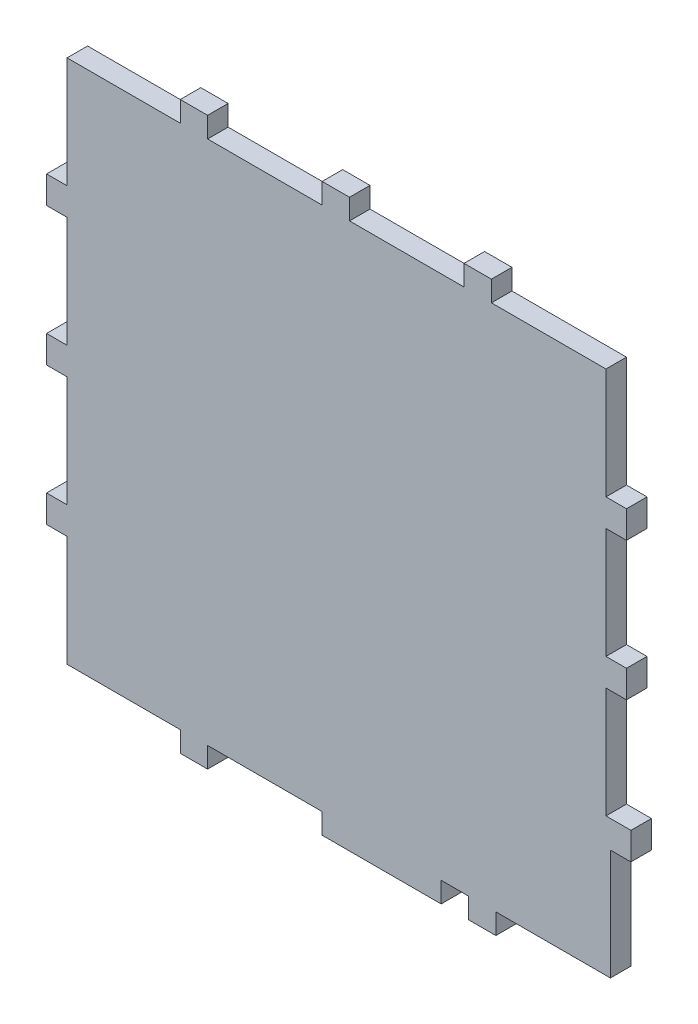
SolidWorks part; units mm, degrees
ref_plane "Front Plane" through (0, 0, 0) normal (0, 0, 1) x (1, 0, 0)
ref_plane "Top Plane" through (0, 0, 0) normal (0, 1, 0) x (1, 0, 0)
ref_plane "Right Plane" through (0, 0, 0) normal (1, 0, 0) x (0, 0, -1)
sketch "Sketch1" plane through (0, 0, 0) normal (0, 0, 1) x (1, 0, 0)
  line L0 (0, 0) -> (0, 81)
  line L1 (0, 81) -> (-15, 81)
  line L2 (-15, 81) -> (-15, 101)
  line L3 (-15, 101) -> (0, 101)
  line L4 (0, 101) -> (0, 182)
  line L5 (0, 182) -> (-15, 182)
  line L6 (-15, 182) -> (-15, 202)
  line L7 (-15, 202) -> (0, 202)
  line L8 (0, 202) -> (0, 283)
  line L9 (0, 283) -> (-15, 283)
  line L10 (-15, 283) -> (-15, 303)
  line L11 (-15, 303) -> (0, 303)
  line L12 (0, 303) -> (0, 384)
  line L13 (0, 384) -> (82.75, 384)
  line L14 (82.75, 384) -> (82.75, 399)
  line L15 (82.75, 399) -> (102.75, 399)
  line L16 (102.75, 399) -> (102.75, 384)
  line L17 (102.75, 384) -> (186.5, 384)
  line L18 (186.5, 384) -> (186.5, 399)
  line L19 (186.5, 399) -> (206.5, 399)
  line L20 (206.5, 399) -> (206.5, 384)
  line L21 (206.5, 384) -> (290.25, 384)
  line L22 (290.25, 384) -> (290.25, 399)
  line L23 (290.25, 399) -> (310.25, 399)
  line L24 (310.25, 399) -> (310.25, 384)
  line L25 (310.25, 384) -> (394, 384)
  line L26 (394, 384) -> (394, 303)
  line L27 (394, 303) -> (409, 303)
  line L28 (409, 303) -> (409, 283)
  line L40 (409, 283) -> (394, 283)
  line L41 (394, 283) -> (394, 202)
  line L42 (394, 202) -> (409, 202)
  line L43 (409, 202) -> (409, 182)
  line L44 (409, 182) -> (394, 182)
  line L45 (394, 182) -> (394, 101)
  line L46 (394, 101) -> (412.25, 101)
  line L47 (412.25, 101) -> (412.25, 81)
  line L48 (412.25, 81) -> (397.25, 81)
  line L49 (397.25, 81) -> (397.25, 0)
  line L51 (0, 0) -> (82.75, 0)
  line L52 (82.75, 0) -> (82.75, -15)
  line L53 (82.75, -15) -> (102.75, -15)
  line L54 (102.75, -15) -> (102.75, 0)
  line L55 (102.75, 0) -> (186.5, 0)
  line L56 (186.5, 0) -> (186.5, -15)
  line L57 (186.5, -15) -> (273.5, -15)
  line L58 (273.5, -15) -> (273.5, 0)
  line L59 (273.5, 0) -> (293.5, 0)
  line L60 (293.5, 0) -> (293.5, -15)
  line L61 (293.5, -15) -> (313.5, -15)
  line L62 (313.5, -15) -> (313.5, 0)
  line L63 (313.5, 0) -> (397.25, 0)
extrude "Boss-Extrude1" add sketch "Sketch1" along normal blind 15
equation "\"ancho\" = 20mm"
equation "\"alto\"= 15mm"
equation "\"separacion\"= 81mm"
equation "\"D9@Sketch1\"=\"ancho\""
equation "\"D8@Sketch1\"=\"alto\""
equation "\"D7@Sketch1\"=\"separacion\""
equation "\"D10@Sketch1\"=\"separacion\""
equation "\"D6@Sketch1\"=\"ancho\""
equation "\"D5@Sketch1\"=\"alto\""
